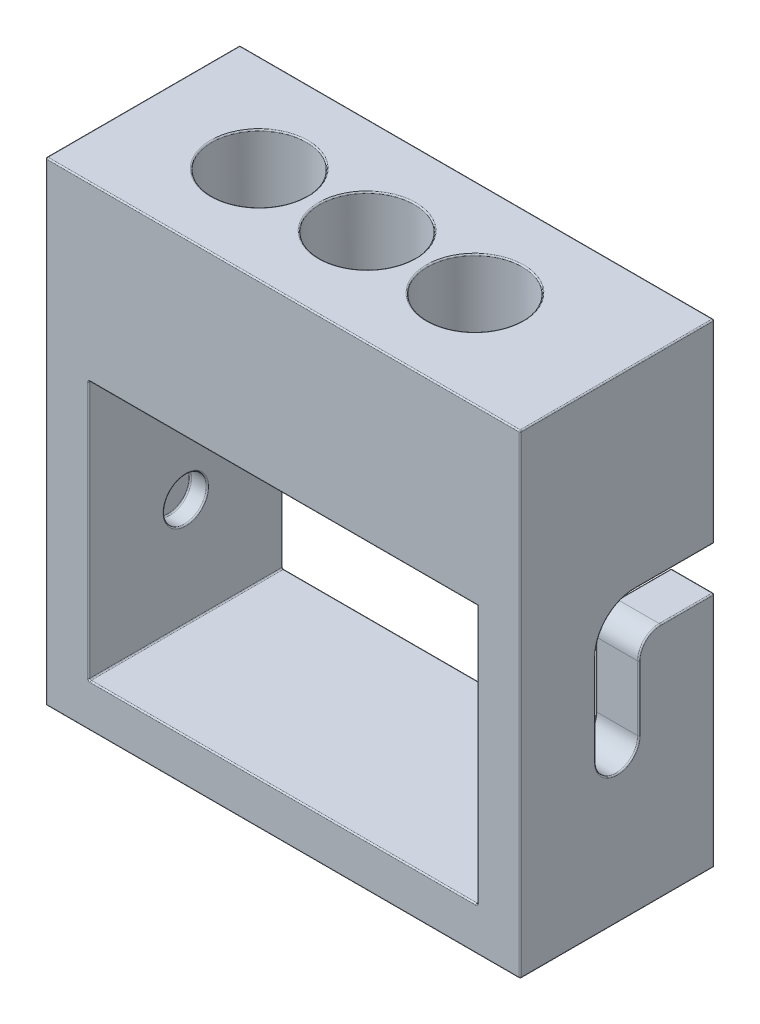
SolidWorks part; units mm, degrees
material "Plain Carbon Steel"
ref_plane "Front Plane" through (0, 0, 0) normal (0, 0, 1) x (1, 0, 0)
ref_plane "Top Plane" through (0, 0, 0) normal (0, 1, 0) x (1, 0, 0)
ref_plane "Right Plane" through (0, 0, 0) normal (1, 0, 0) x (0, 0, -1)
other "Configuration Table"
sketch "Sketch1" plane through (0, 0, 0) normal (0, 0, 1) x (1, 0, 0)
  line L0 (88.9, 0) -> (139.7, 0)
  line L1 (0, 0) -> (12.7, 0)
  line L2 (0, 0) -> (0, 139.7)
  line L3 (0, 139.7) -> (139.7, 139.7)
  line L4 (139.7, 0) -> (139.7, 139.7)
  line L6 (12.7, 12.7) -> (12.7, 88.9)
  line L7 (12.7, 88.9) -> (127, 88.9)
  line L8 (127, 12.7) -> (127, 88.9)
  line L10 (12.7, 0) -> (88.9, 0)
  line L12 (12.7, 12.7) -> (127, 12.7)
  dimension "D1" = 139.7
  dimension "D2" = 139.7
  dimension "D3" = 50.8
  dimension "D4" = 12.7
  dimension "D5" = 12.7
  dimension "D6" = 12.7
extrude "Boss-Extrude1" add sketch "Sketch1" along normal mid plane 57.15
sketch "Sketch2" plane through (0, 139.7, 0) normal (0, 1, 0) x (1, 0, 0)
  line L0 (-76.835, 0) -> (76.835, 0) construction
  line L1 (0, -31.4325) -> (0, 31.4325) construction
  circle A0 centre (66.04, 0) radius 13.97
  circle A1 centre (34.29, 0) radius 13.97
  circle A2 centre (97.79, 0) radius 13.97
  dimension "D1" = 27.94
  dimension "D2" = 66.04
  dimension "D3" = 34.29
  dimension "D4" = 97.79
extrude "Cut-Extrude1" cut sketch "Sketch2" against normal blind 88.9
sketch "Sketch3" plane through (139.7, 0, 0) normal (1, 0, 0) x (0, 0, -1)
  line L0 (0, 76.835) -> (0, -76.835) construction
  line L1 (31.4325, 0) -> (-31.4325, 0) construction
  circle A0 centre (0, 44.45) radius 6.35
  dimension "D1" = 12.7
  dimension "D2" = 44.45
extrude "Cut-Extrude2" cut sketch "Sketch3" against normal blind 132.08
sketch "Sketch4" plane through (0, 88.9, 0) normal (0, -1, 0) x (1, 0, 0)
  line L0 (0, 28.575) -> (0, -28.575) construction
  line L1 (12.7, -22.225) -> (127, -22.225)
  line L2 (12.7, -22.225) -> (12.7, 22.225)
  line L3 (12.7, 22.225) -> (127, 22.225)
  line L4 (127, -22.225) -> (127, 22.225)
  line L5 (139.7, 28.575) -> (139.7, -28.575) construction
  line L6 (0, 28.575) -> (139.7, 28.575) construction
  line L7 (0, -28.575) -> (139.7, -28.575) construction
  dimension "D1" = 12.7
  dimension "D2" = 12.7
  dimension "D3" = 6.35
  dimension "D4" = 6.35
extrude "Cut-Extrude3" cut sketch "Sketch4" against normal blind 19.05
sketch "Sketch5" plane through (139.7, 0, 0) normal (1, 0, 0) x (0, 0, -1)
  line L0 (-6.35, 44.45) -> (-6.35, 71.12)
  line L1 (5.08, 82.55) -> (28.575, 82.55)
  line L2 (28.575, 0) -> (28.575, 139.7) construction
  line L3 (6.35, 44.45) -> (6.35, 63.5)
  line L4 (12.7, 69.85) -> (28.575, 69.85)
  line L5 (28.575, 69.85) -> (28.575, 82.55)
  circle A0 centre (0, 44.45) radius 6.35 construction
  arc A1 (-6.35, 44.45) -> (6.35, 44.45) centre (0, 44.45) ccw
  arc A2 (-6.35, 71.12) -> (5.08, 82.55) centre (5.08, 71.12) cw
  arc A3 (6.35, 63.5) -> (12.7, 69.85) centre (12.7, 63.5) cw
  point P15 (-6.35, 82.55)
  dimension "D1" = 12.7
  dimension "D3" = 11.43
  dimension "D4" = 6.35
  dimension "D2" = 38.1
extrude "Cut-Extrude4" cut sketch "Sketch5" against normal blind 25.4
fillet "Fillet1" radius 0.381 53 edges at (127, 85.725, -28.575) (127, 88.9, -25.4) (69.85, 88.9, -28.575) (127, 41.275, -28.575) (127, 82.55, -16.8275) (127, 79.2022, 3.0022) (127, 57.785, 6.35) (139.7, 53.975, -6.35) (139.7, 67.9901, -8.2099) (139.7, 69.85, -20.6375) (139.7, 82.55, -16.8275) (139.7, 79.2022, 3.0022) (139.7, 57.785, 6.35) (133.35, 69.85, -28.575) (127, 53.975, -6.35) (69.85, 88.9, -22.225) (12.7, 107.95, 0) (69.85, 107.95, -22.225) (12.7, 98.425, -22.225) (127, 98.425, -22.225) (12.7, 98.425, 22.225) (97.79, 107.95, 13.97) (34.29, 107.95, 13.97) (66.04, 107.95, 13.97) (139.7, 38.1, 0) (7.62, 44.45, -6.35) (12.7, 44.45, -6.35) (127, 38.1, 0) (97.79, 139.7, 13.97) (34.29, 139.7, 13.97) (66.04, 139.7, 13.97) (12.7, 50.8, -28.575) (69.85, 12.7, -28.575) (127, 50.8, 28.575) (69.85, 88.9, 28.575) (12.7, 50.8, 28.575) (69.85, 12.7, 28.575) (127, 12.7, 0) (12.7, 12.7, 0) (12.7, 88.9, -25.4) (12.7, 88.9, 25.4) (139.7, 111.125, -28.575) (139.7, 34.925, -28.575) (69.85, 139.7, -28.575) (0, 69.85, 28.575) (69.85, 0, 28.575) (139.7, 69.85, 28.575) (69.85, 139.7, 28.575) (0, 139.7, 0) (139.7, 139.7, 0) (139.7, 0, 0) (127, 67.9901, -8.2099) (127, 69.85, -20.6375)
